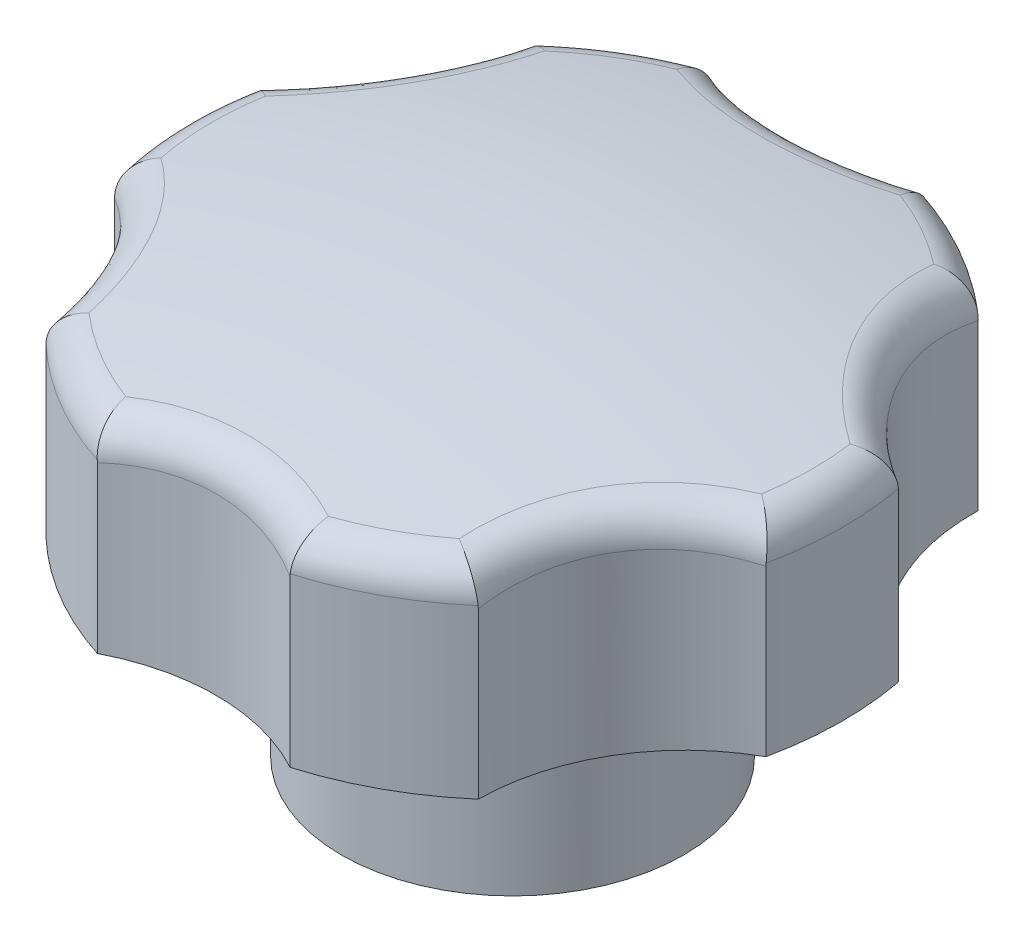
SolidWorks part; units mm, degrees
ref_plane "정면" through (0, 0, 0) normal (0, 0, 1) x (1, 0, 0)
ref_plane "윗면" through (0, 0, 0) normal (0, 1, 0) x (1, 0, 0)
ref_plane "우측면" through (0, 0, 0) normal (1, 0, 0) x (0, 0, -1)
sketch "스케치1" plane through (0, 0, 0) normal (0, 1, 0) x (1, 0, 0)
  line L0 (0, 0) -> (66.8706, 38.6078) construction
  line L1 (-75.222, 0) -> (91.2112, 0) construction
  line L2 (0, 90.4234) -> (0, -97.3307) construction
  line L3 (0, 0) -> (-66.8706, 38.6078) construction
  circle A0 centre (0, 0) radius 27
  circle A1 centre (0, 0) radius 40 construction
  dimension "D1" = 54
  dimension "D2" = 80
  dimension "D3" = 60
extrude "보스-돌출1" add sketch "스케치1" along normal blind 19
sketch "스케치2" plane through (0, 19, 0) normal (0, 1, 0) x (1, 0, 0)
  line L0 (0, 0) -> (0, 40) construction
  line L1 (0, 0) -> (40, 0) construction
  line L2 (0, 0) -> (34.641, 20) construction
  circle A0 centre (0, 0) radius 40 construction
  circle A1 centre (34.641, 20) radius 17
  dimension "D1" = 80
  dimension "D3" = 34
  dimension "D2" = 60
extrude "컷-돌출1" cut sketch "스케치2" against normal through all contours A1
pattern_circular "원형 패턴1" count 6 over 360 about axis through (-0.4642, 0, 0.268) along (0, 1, 0) of "컷-돌출1"
sketch "스케치3" plane through (0, 0, 0) normal (0, 0, 1) x (1, 0, 0)
  line L0 (7.6835, 19) -> (-8.2703, 19) construction
  line L2 (0, 29) -> (27, 29)
  line L3 (27, 29) -> (27, 16.1652)
  line L4 (27, 0) -> (27, 19) construction
  line L6 (26.3984, 19) -> (17.6413, 19) construction
  line L7 (0, 19) -> (0, 29)
  arc A0 (27, 16.1652) -> (0, 19) centre (0, -111) ccw
  point P2 (-6.093, 18.8571)
  dimension "D1" = 260
  dimension "D2" = 10
ref_axis "기준축1" through (0, 19, 0) along (0, -1, 0)
revolve "컷-회전2" cut sketch "스케치3" angle 360 about axis through (0, 19, 0) along (0, -1, 0)
sketch "스케치4" plane through (0, 0, 0) normal (0, -1, 0) x (1, 0, 0)
  circle A0 centre (0, 0) radius 14
  dimension "D1" = 28
extrude "보스-돌출2" add sketch "스케치4" along normal blind 16
hole_wizard "M1 여유 구멍1" positions "스케치7" profile "스케치6" hole size "M1" standard "KS"
sketch "스케치7" plane through (0, -16, 0) normal (0, -1, 0) x (-1, 0, 0)
  point P0 (0, 0)
sketch "스케치6" plane through (0, -16, 0) normal (1, 0, 0) x (0, 0, -1)
  line L0 (0, 0) -> (0, 23.0043)
  line L1 (0, 23.0043) -> (5, 20)
  line L2 (5, 20) -> (5, 0)
  line L5 (5, 0) -> (0, 0)
  line L10 (0, 23.0043) -> (-5, 20) construction
  line L11 (0, -6.35) -> (0, 107.95) construction
  dimension "구멍 지름" = 10
  dimension "구멍 깊이" = 20
  dimension "드릴 각도" = 118
sketch "스케치9" plane through (0, 0, 0) normal (1, 0, 0) x (0, 0, -1)
  line L0 (-14, -16) -> (14, -16) construction
  circle A0 centre (0, -6) radius 1.5
  point P2 (0, -4.6575)
  point P5 (-14, -6)
  dimension "D2" = 3
  dimension "D1" = 10
extrude "컷-돌출2" cut sketch "스케치9" against normal through all both and the other way through all
fillet "필렛1" radius 3 13 edges at (0, 0, -14) (12.9517, 16.1652, 23.6908) (26.9982, 16.1652, 0.3077) (21.1641, 16.8615, 10.1739) (-13.7784, 16.1652, 23.2197) (-3.0744, 16.7274, 24.0055) (-26.9981, 16.1652, 0.3225) (-22.2243, 16.6949, 10.0046) (-14.041, 16.1652, -23.0619) (-19.5808, 16.7274, -14.2236) (13.2327, 16.1652, -23.535) (-2.3104, 16.8615, -23.3685) (19.1321, 16.9218, -13.0377)
ref_plane "평면1" through (0, 0, 0) normal (1, 0, 0) x (0, 0, -1)
ref_plane "평면2" through (0, 0, 0) normal (0, 1, 0) x (1, 0, 0)
ref_plane "평면3" through (0, 0, 0) normal (0, 0, 1) x (1, 0, 0)
